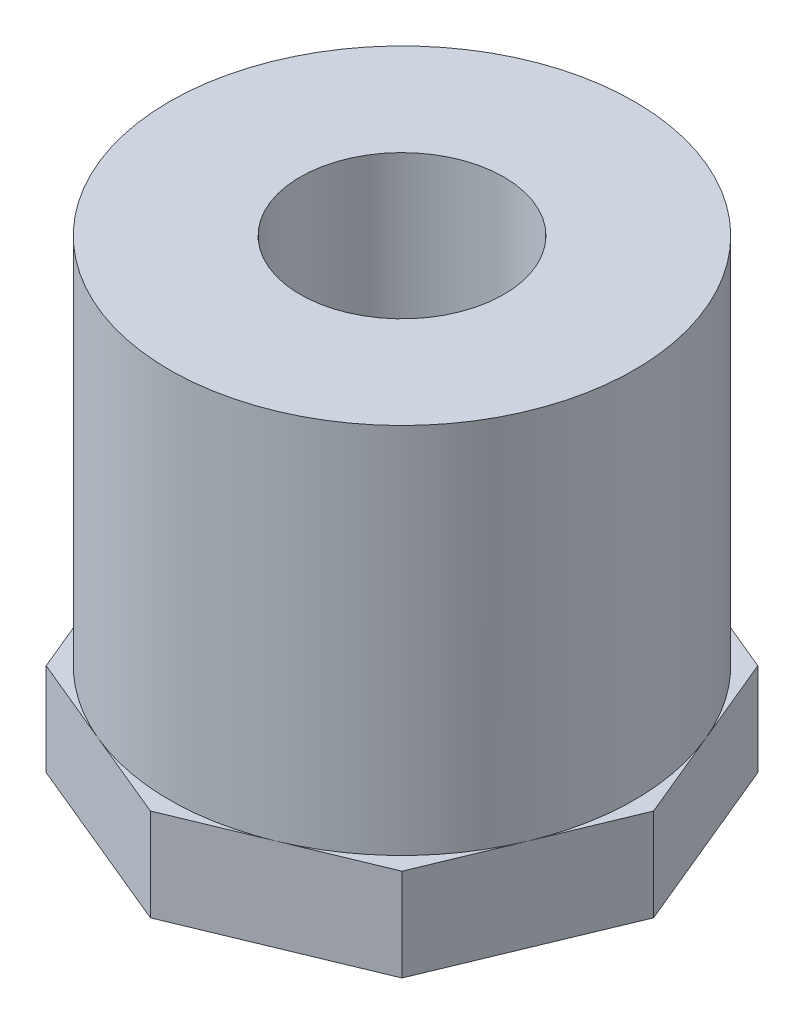
SolidWorks part; units mm, degrees
ref_plane "Front" through (0, 0, 0) normal (0, 0, 1) x (1, 0, 0)
ref_plane "Top" through (0, 0, 0) normal (0, 1, 0) x (1, 0, 0)
ref_plane "Right" through (0, 0, 0) normal (1, 0, 0) x (0, 0, -1)
sketch "Sketch1" plane through (0, 0, 0) normal (0, 0, 1) x (1, 0, 0)
  line L0 (0, 0) -> (0, 25.4)
  line L1 (0, 25.4) -> (-12.7, 25.4)
  line L2 (-12.7, 25.4) -> (-12.7, 0)
  line L5 (-12.7, 0) -> (0, 0)
  line L6 (0, 0) -> (0, -9.8334) construction
  dimension "D1" = 25.4
  dimension "D3" = 25.4
revolve "Revolve1" add sketch "Sketch1" angle 360 about L6
sketch "Sketch2" plane through (0, 0, 0) normal (0, -1, 0) x (1, 0, 0)
  line L1 (0, 13.7464) -> (-9.7202, 9.7202)
  line L2 (-9.7202, 9.7202) -> (-13.7464, 0)
  line L3 (-13.7464, 0) -> (-9.7202, -9.7202)
  line L4 (-9.7202, -9.7202) -> (0, -13.7464)
  line L5 (0, -13.7464) -> (9.7202, -9.7202)
  line L6 (9.7202, -9.7202) -> (13.7464, 0)
  line L7 (13.7464, 0) -> (9.7202, 9.7202)
  line L8 (9.7202, 9.7202) -> (0, 13.7464)
  circle A0 centre (0, 0) radius 12.7 construction
  circle A1 centre (0, 0) radius 12.7 construction
extrude "Boss-Extrude1" add sketch "Sketch2" against normal blind 5.0546
hole_wizard "1/4 NPT Tapped Hole1" positions "Sketch3" profile "Sketch4" size "1/4" standard "ANSI Inch" end condition through all
sketch "Sketch3" plane through (0, 0, 0) normal (0, -1, 0) x (-1, 0, 0)
  point P3 (0, 0)
sketch "Sketch4" plane through (0, 0, 0) normal (1, 0, 0) x (0, 0, -1)
  line L0 (0, 0) -> (0, 25.4)
  line L1 (0, 25.4) -> (5.5626, 25.4)
  line L2 (-5.9437, 10.0203) -> (-6.2437, 0) construction
  line L3 (5.5626, 25.4) -> (5.5626, 10.0203)
  line L4 (5.5626, 10.0203) -> (5.9437, 10.0203)
  line L5 (5.9437, 10.0203) -> (6.2437, 0)
  line L7 (6.2437, 0) -> (0, 0)
  line L8 (0, -6.35) -> (0, 107.95) construction
  line L11 (-5.5626, 10.0203) -> (-5.9437, 10.0203) construction
  dimension "Thru Tap Drill Dia." = 11.1252
  dimension "Thru Tap Drill Depth" = 25.4
  dimension "Thread Dia." = 12.4874
  dimension "Thread Angle" = 3.43
  dimension "Thread Depth" = 10.0203
cosmetic thread "Hole Thread1"
